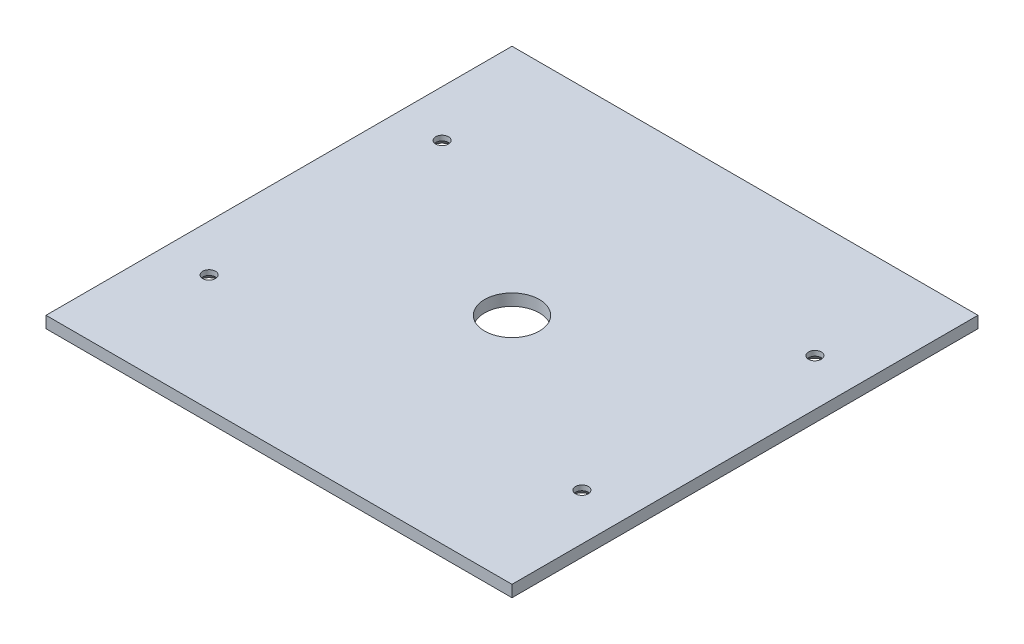
SolidWorks part; units mm, degrees
material "Plain Carbon Steel"
ref_plane "Front" through (0, 0, 0) normal (0, 0, 1) x (1, 0, 0)
ref_plane "Top" through (0, 0, 0) normal (0, 1, 0) x (1, 0, 0)
ref_plane "Right" through (0, 0, 0) normal (1, 0, 0) x (0, 0, -1)
sketch "Sketch1" plane through (0, 0, 0) normal (0, 1, 0) x (1, 0, 0)
  line L1 (0, 0) -> (-200, 0)
  line L2 (0, 0) -> (0, 200)
  line L3 (0, 200) -> (-200, 200)
  line L4 (-200, 0) -> (-200, 200)
  dimension "D1" = 200
  dimension "D2" = 200
extrude "Boss-Extrude1" add sketch "Sketch1" along normal blind 5
hole_wizard "CSK for M5 Countersunk Flat Head Screw1" positions "Sketch3" profile "Sketch4" countersink size "M5" standard "ISO"
sketch "Sketch3" plane through (0, 0, 0) normal (0, -1, 0) x (-1, 0, 0)
  line L0 (0, 0) -> (0, 200) construction
  line L1 (200, 0) -> (0, 0) construction
  line L2 (0, 0) -> (0, 200) construction
  point P0 (180, 50)
  point P2 (180, 150)
  point P5 (20, 50)
  point P8 (20, 150)
  dimension "D1" = 100
  dimension "D2" = 160
  dimension "D3" = 100
  dimension "D4" = 160
  dimension "D5" = 20
  dimension "D6" = 50
  dimension "D7" = 20
  dimension "D8" = 0
sketch "Sketch4" plane through (-180, 0, -50) normal (1, 0, 0) x (0, 0, -1)
  line L0 (0, 0) -> (0, 11.6524)
  line L1 (0, 11.6524) -> (2.75, 10)
  line L2 (2.75, 10) -> (2.75, 2.85)
  line L3 (2.75, 2.85) -> (5.6, 0)
  line L5 (5.6, 0) -> (0, 0)
  line L6 (-2.75, 2.85) -> (-5.6, 0) construction
  line L10 (0, 11.6524) -> (-2.75, 10) construction
  line L11 (0, -6.35) -> (0, 107.95) construction
  dimension "Hole Dia." = 5.5
  dimension "Hole Depth" = 10
  dimension "Near C'Sink Dia." = 11.2
  dimension "Near C'Sink Angle" = 90
  dimension "Drill Angle" = 118
sketch "Sketch5" plane through (0, 0, 0) normal (0, -1, 0) x (1, 0, 0)
  line L0 (0, 0) -> (0, -200) construction
  line L7 (-200, 0) -> (0, 0) construction
  circle A4 centre (-100, -100) radius 11.75
  point P0 (-100, -100)
  point P5 (0, -100)
  dimension "D1" = 0
  dimension "D3" = 100
  dimension "D4" = 100
extrude "Cut-Extrude1" cut sketch "Sketch5" against normal blind 10
